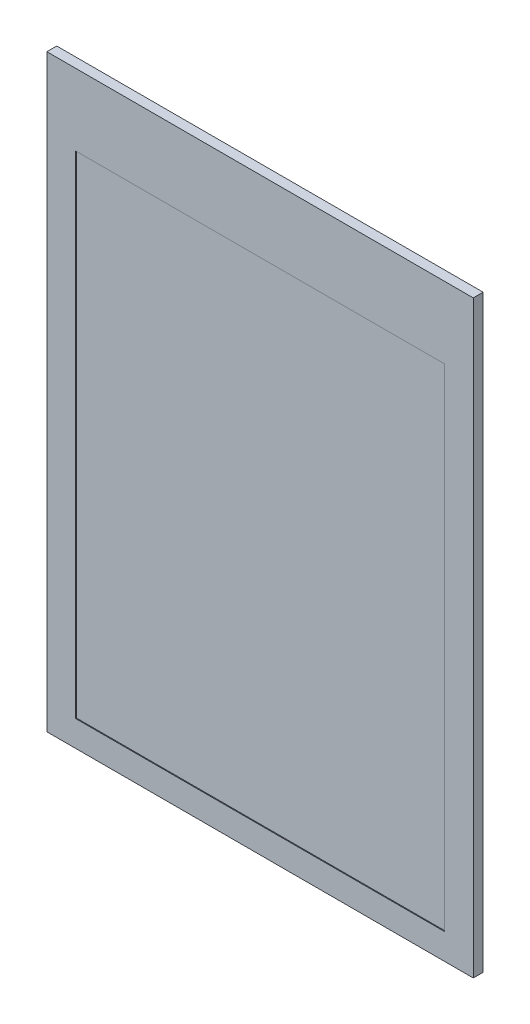
SolidWorks part; units mm, degrees
ref_plane "Front Plane" through (0, 0, 0) normal (0, 0, 1) x (1, 0, 0)
ref_plane "Top Plane" through (0, 0, 0) normal (0, 1, 0) x (1, 0, 0)
ref_plane "Right Plane" through (0, 0, 0) normal (1, 0, 0) x (0, 0, -1)
sketch "Sketch1" plane through (0, 0, 8.7925) normal (0, 0, 1) x (1, 0, 0)
  line L1 (27.238, -26.9222) -> (-22.7238, -26.9222)
  line L2 (27.238, -26.9222) -> (27.238, -95.934)
  line L3 (27.238, -95.934) -> (-22.7238, -95.934)
  line L4 (-22.7238, -26.9222) -> (-22.7238, -95.934)
extrude "Boss-Extrude1" add sketch "Sketch1" along normal offset from surface (1.1566 mm away) 5.5
sketch "Sketch3" plane through (0, 0, 9.9491) normal (0, 0, 1) x (1, 0, 0)
  line L1 (23.8569, -35.3042) -> (-19.3429, -35.3042)
  line L2 (23.8569, -35.3042) -> (23.8569, -92.9039)
  line L3 (23.8569, -92.9039) -> (-19.3429, -92.9039)
  line L4 (-19.3429, -35.3042) -> (-19.3429, -92.9039)
extrude "Cut-Extrude1" cut sketch "Sketch3" against normal blind 0.1
